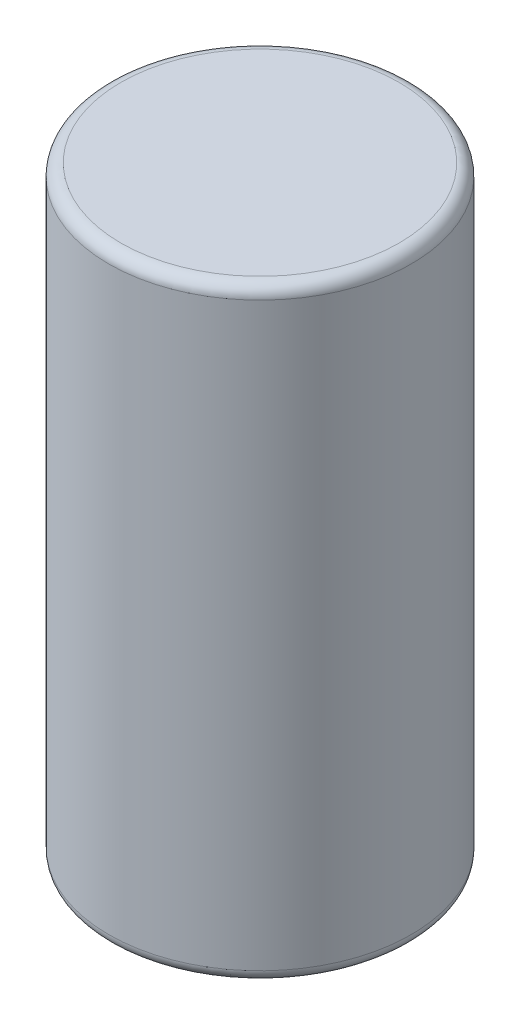
SolidWorks part; units mm, degrees
ref_plane "Front Plane" through (0, 0, 0) normal (0, 0, 1) x (1, 0, 0)
ref_plane "Top Plane" through (0, 0, 0) normal (0, 1, 0) x (1, 0, 0)
ref_plane "Right Plane" through (0, 0, 0) normal (1, 0, 0) x (0, 0, -1)
sketch "Sketch1" plane through (0, 0, 0) normal (0, 0, 1) x (1, 0, 0)
  line L0 (2.921, 6.35) -> (0, 6.35)
  line L1 (0, 6.35) -> (0, -6.35)
  line L2 (0, -6.35) -> (2.921, -6.35)
  line L3 (3.175, -6.096) -> (3.175, 6.096)
  line L4 (0, 6.35) -> (0, -6.35) construction
  arc A0 (2.921, -6.35) -> (3.175, -6.096) centre (2.921, -6.096) ccw
  arc A1 (3.175, 6.096) -> (2.921, 6.35) centre (2.921, 6.096) ccw
revolve "Revolve1" add sketch "Sketch1" angle 360 about L4
